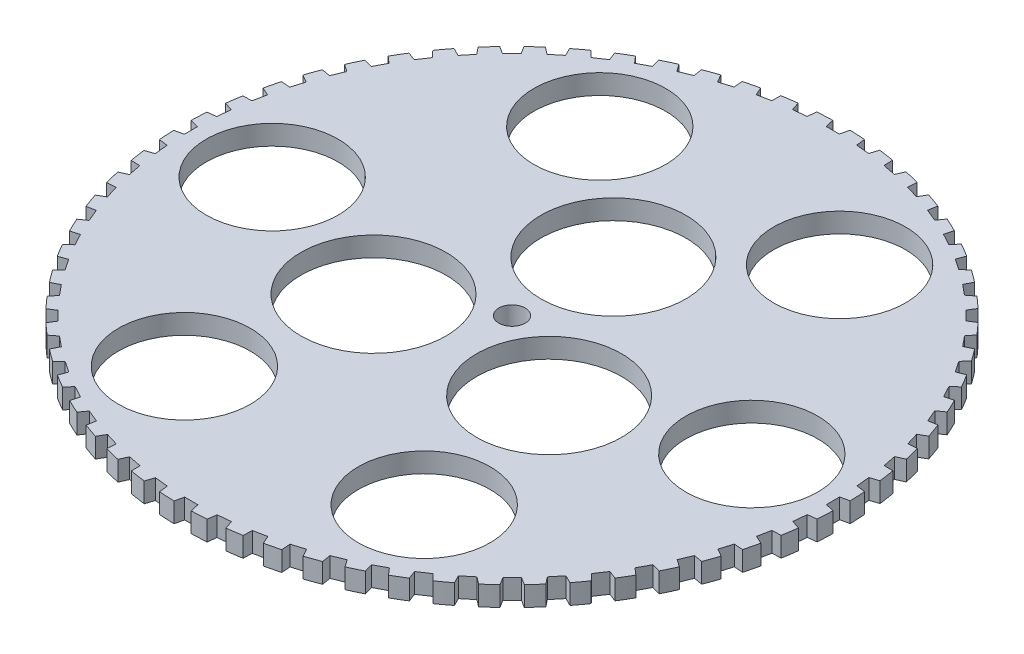
SolidWorks part; units mm, degrees
ref_plane "Plan de face" through (0, 0, 0) normal (0, 0, 1) x (1, 0, 0)
ref_plane "Plan de dessus" through (0, 0, 0) normal (0, 1, 0) x (1, 0, 0)
ref_plane "Plan de droite" through (0, 0, 0) normal (1, 0, 0) x (0, 0, -1)
sketch "Esquisse1" plane through (0, 0, 0) normal (0, 1, 0) x (1, 0, 0)
  circle A0 centre (0, 0) radius 50
  circle A1 centre (36.3777, 0) radius 10
  circle A2 centre (18.1888, -31.504) radius 10
  circle A3 centre (-18.1888, -31.504) radius 10
  circle A4 centre (-36.3777, 0) radius 10
  circle A5 centre (-18.1888, 31.504) radius 10
  circle A6 centre (18.1888, 31.504) radius 10
  circle A7 centre (0, 15.3792) radius 11
  circle A8 centre (13.3188, -7.6896) radius 11
  circle A9 centre (-13.3188, -7.6896) radius 11
  circle A10 centre (0, 0) radius 2
  dimension "D1" = 100
extrude "Extrusion1" add sketch "Esquisse1" along normal blind 3
sketch "Esquisse3" plane through (0, 3, 0) normal (0, 1, 0) x (1, 0, 0)
  line L0 (-3.4533, -50.9425) -> (-6.5125, -50.6412)
  line L1 (1.022, -48.6717) -> (-0.9823, -48.6717)
  line L2 (1.022, -48.6717) -> (1.5566, -51.0357)
  line L3 (1.5566, -51.0357) -> (-1.5174, -51.0357)
  line L4 (-0.9823, -48.6717) -> (-1.5174, -51.0357)
  line L5 (-5.7482, -48.341) -> (-6.5125, -50.6412)
  line L6 (-3.7536, -48.5375) -> (-5.7482, -48.341)
  line L7 (-3.7536, -48.5375) -> (-3.4533, -50.9425)
  line L8 (-8.4299, -50.3587) -> (-11.4448, -49.759)
  line L9 (-10.4588, -47.5448) -> (-11.4448, -49.759)
  line L10 (-8.4931, -47.9358) -> (-10.4588, -47.5448)
  line L11 (-8.4931, -47.9358) -> (-8.4299, -50.3587)
  line L12 (-13.3253, -49.2899) -> (-16.2669, -48.3976)
  line L13 (-15.0686, -46.2908) -> (-16.2669, -48.3976)
  line L14 (-13.1507, -46.8726) -> (-15.0686, -46.2908)
  line L15 (-13.1507, -46.8726) -> (-13.3253, -49.2899)
  line L16 (-18.0924, -47.7465) -> (-20.9324, -46.5701)
  line L17 (-19.5334, -44.5909) -> (-20.9324, -46.5701)
  line L18 (-17.6817, -45.3579) -> (-19.5334, -44.5909)
  line L19 (-17.6817, -45.3579) -> (-18.0924, -47.7465)
  line L20 (-22.6853, -45.7432) -> (-25.3963, -44.2941)
  line L21 (-23.81, -42.4615) -> (-25.3963, -44.2941)
  line L22 (-22.0424, -43.4063) -> (-23.81, -42.4615)
  line L23 (-22.0424, -43.4063) -> (-22.6853, -45.7432)
  line L24 (-27.0597, -43.2994) -> (-29.6156, -41.5916)
  line L25 (-27.8573, -39.9233) -> (-29.6156, -41.5916)
  line L26 (-26.1908, -41.0368) -> (-27.8573, -39.9233)
  line L27 (-26.1908, -41.0368) -> (-27.0597, -43.2994)
  line L28 (-31.1735, -40.4386) -> (-33.5497, -38.4885)
  line L29 (-31.6363, -37.0006) -> (-33.5497, -38.4885)
  line L30 (-30.087, -38.272) -> (-31.6363, -37.0006)
  line L31 (-30.087, -38.272) -> (-31.1735, -40.4386)
  line L32 (-34.987, -37.1883) -> (-37.1606, -35.0147)
  line L33 (-35.1107, -33.7215) -> (-37.1606, -35.0147)
  line L34 (-33.6934, -35.1387) -> (-35.1107, -33.7215)
  line L35 (-33.6934, -35.1387) -> (-34.987, -37.1883)
  line L36 (-38.4636, -33.5799) -> (-40.4137, -31.2037)
  line L37 (-38.2469, -30.1177) -> (-40.4137, -31.2037)
  line L38 (-36.9754, -31.667) -> (-38.2469, -30.1177)
  line L39 (-36.9754, -31.667) -> (-38.4636, -33.5799)
  line L40 (-41.5698, -29.6481) -> (-43.2776, -27.0922)
  line L41 (-41.0148, -26.2238) -> (-43.2776, -27.0922)
  line L42 (-39.9013, -27.8903) -> (-41.0148, -26.2238)
  line L43 (-39.9013, -27.8903) -> (-41.5698, -29.6481)
  line L44 (-44.2757, -25.4308) -> (-45.7247, -22.7198)
  line L45 (-43.3876, -22.0774) -> (-45.7247, -22.7198)
  line L46 (-42.4428, -23.845) -> (-43.3876, -22.0774)
  line L47 (-42.4428, -23.845) -> (-44.2757, -25.4308)
  line L48 (-46.5551, -20.9686) -> (-47.7315, -18.1286)
  line L49 (-45.3427, -17.7183) -> (-47.7315, -18.1286)
  line L50 (-44.5757, -19.57) -> (-45.3427, -17.7183)
  line L51 (-44.5757, -19.57) -> (-46.5551, -20.9686)
  line L52 (-48.3863, -16.3044) -> (-49.2786, -13.3628)
  line L53 (-46.861, -13.1886) -> (-49.2786, -13.3628)
  line L54 (-46.2792, -15.1066) -> (-46.861, -13.1886)
  line L55 (-46.2792, -15.1066) -> (-48.3863, -16.3044)
  line L56 (-49.7514, -11.4832) -> (-50.3511, -8.4683)
  line L57 (-47.9281, -8.532) -> (-50.3511, -8.4683)
  line L58 (-47.5371, -10.4977) -> (-47.9281, -8.532)
  line L59 (-47.5371, -10.4977) -> (-49.7514, -11.4832)
  line L60 (-50.6374, -6.5514) -> (-50.9387, -3.4923)
  line L61 (-48.5336, -3.7931) -> (-50.9387, -3.4923)
  line L62 (-48.3371, -5.7877) -> (-48.5336, -3.7931)
  line L63 (-48.3371, -5.7877) -> (-50.6374, -6.5514)
  line L64 (-51.0357, -1.5566) -> (-51.0357, 1.5174)
  line L65 (-48.6717, 0.9823) -> (-51.0357, 1.5174)
  line L66 (-48.6717, -1.022) -> (-48.6717, 0.9823)
  line L67 (-48.6717, -1.022) -> (-51.0357, -1.5566)
  line L68 (-50.9425, 3.4533) -> (-50.6412, 6.5125)
  line L69 (-48.341, 5.7482) -> (-50.6412, 6.5125)
  line L70 (-48.5375, 3.7536) -> (-48.341, 5.7482)
  line L71 (-48.5375, 3.7536) -> (-50.9425, 3.4533)
  line L72 (-50.3587, 8.4299) -> (-49.759, 11.4448)
  line L73 (-47.5448, 10.4588) -> (-49.759, 11.4448)
  line L74 (-47.9358, 8.4931) -> (-47.5448, 10.4588)
  line L75 (-47.9358, 8.4931) -> (-50.3587, 8.4299)
  line L76 (-49.2899, 13.3253) -> (-48.3976, 16.2669)
  line L77 (-46.2908, 15.0686) -> (-48.3976, 16.2669)
  line L78 (-46.8726, 13.1507) -> (-46.2908, 15.0686)
  line L79 (-46.8726, 13.1507) -> (-49.2899, 13.3253)
  line L80 (-47.7465, 18.0924) -> (-46.5701, 20.9324)
  line L81 (-44.5909, 19.5334) -> (-46.5701, 20.9324)
  line L82 (-45.3579, 17.6817) -> (-44.5909, 19.5334)
  line L83 (-45.3579, 17.6817) -> (-47.7465, 18.0924)
  line L84 (-45.7432, 22.6853) -> (-44.2941, 25.3963)
  line L85 (-42.4615, 23.81) -> (-44.2941, 25.3963)
  line L86 (-43.4063, 22.0424) -> (-42.4615, 23.81)
  line L87 (-43.4063, 22.0424) -> (-45.7432, 22.6853)
  line L88 (-43.2994, 27.0597) -> (-41.5916, 29.6156)
  line L89 (-39.9233, 27.8573) -> (-41.5916, 29.6156)
  line L90 (-41.0368, 26.1908) -> (-39.9233, 27.8573)
  line L91 (-41.0368, 26.1908) -> (-43.2994, 27.0597)
  line L92 (-40.4386, 31.1735) -> (-38.4885, 33.5497)
  line L93 (-37.0006, 31.6363) -> (-38.4885, 33.5497)
  line L94 (-38.272, 30.087) -> (-37.0006, 31.6363)
  line L95 (-38.272, 30.087) -> (-40.4386, 31.1735)
  line L96 (-37.1883, 34.987) -> (-35.0147, 37.1606)
  line L97 (-33.7215, 35.1107) -> (-35.0147, 37.1606)
  line L98 (-35.1387, 33.6934) -> (-33.7215, 35.1107)
  line L99 (-35.1387, 33.6934) -> (-37.1883, 34.987)
  line L100 (-33.5799, 38.4636) -> (-31.2037, 40.4137)
  line L101 (-30.1177, 38.2469) -> (-31.2037, 40.4137)
  line L102 (-31.667, 36.9754) -> (-30.1177, 38.2469)
  line L103 (-31.667, 36.9754) -> (-33.5799, 38.4636)
  line L104 (-29.6481, 41.5698) -> (-27.0922, 43.2776)
  line L105 (-26.2238, 41.0148) -> (-27.0922, 43.2776)
  line L106 (-27.8903, 39.9013) -> (-26.2238, 41.0148)
  line L107 (-27.8903, 39.9013) -> (-29.6481, 41.5698)
  line L108 (-25.4308, 44.2757) -> (-22.7198, 45.7247)
  line L109 (-22.0774, 43.3876) -> (-22.7198, 45.7247)
  line L110 (-23.845, 42.4428) -> (-22.0774, 43.3876)
  line L111 (-23.845, 42.4428) -> (-25.4308, 44.2757)
  line L112 (-20.9686, 46.5551) -> (-18.1286, 47.7315)
  line L113 (-17.7183, 45.3427) -> (-18.1286, 47.7315)
  line L114 (-19.57, 44.5757) -> (-17.7183, 45.3427)
  line L115 (-19.57, 44.5757) -> (-20.9686, 46.5551)
  line L116 (-16.3044, 48.3863) -> (-13.3628, 49.2786)
  line L117 (-13.1886, 46.861) -> (-13.3628, 49.2786)
  line L118 (-15.1066, 46.2792) -> (-13.1886, 46.861)
  line L119 (-15.1066, 46.2792) -> (-16.3044, 48.3863)
  line L120 (-11.4832, 49.7514) -> (-8.4683, 50.3511)
  line L121 (-8.532, 47.9281) -> (-8.4683, 50.3511)
  line L122 (-10.4977, 47.5371) -> (-8.532, 47.9281)
  line L123 (-10.4977, 47.5371) -> (-11.4832, 49.7514)
  line L124 (-6.5514, 50.6374) -> (-3.4923, 50.9387)
  line L125 (-3.7931, 48.5336) -> (-3.4923, 50.9387)
  line L126 (-5.7877, 48.3371) -> (-3.7931, 48.5336)
  line L127 (-5.7877, 48.3371) -> (-6.5514, 50.6374)
  line L128 (-1.5566, 51.0357) -> (1.5174, 51.0357)
  line L129 (0.9823, 48.6717) -> (1.5174, 51.0357)
  line L130 (-1.022, 48.6717) -> (0.9823, 48.6717)
  line L131 (-1.022, 48.6717) -> (-1.5566, 51.0357)
  line L132 (3.4533, 50.9425) -> (6.5125, 50.6412)
  line L133 (5.7482, 48.341) -> (6.5125, 50.6412)
  line L134 (3.7536, 48.5375) -> (5.7482, 48.341)
  line L135 (3.7536, 48.5375) -> (3.4533, 50.9425)
  line L136 (8.4299, 50.3587) -> (11.4448, 49.759)
  line L137 (10.4588, 47.5448) -> (11.4448, 49.759)
  line L138 (8.4931, 47.9358) -> (10.4588, 47.5448)
  line L139 (8.4931, 47.9358) -> (8.4299, 50.3587)
  line L140 (13.3253, 49.2899) -> (16.2669, 48.3976)
  line L141 (15.0686, 46.2908) -> (16.2669, 48.3976)
  line L142 (13.1507, 46.8726) -> (15.0686, 46.2908)
  line L143 (13.1507, 46.8726) -> (13.3253, 49.2899)
  line L144 (18.0924, 47.7465) -> (20.9324, 46.5701)
  line L145 (19.5334, 44.5909) -> (20.9324, 46.5701)
  line L146 (17.6817, 45.3579) -> (19.5334, 44.5909)
  line L147 (17.6817, 45.3579) -> (18.0924, 47.7465)
  line L148 (22.6853, 45.7432) -> (25.3963, 44.2941)
  line L149 (23.81, 42.4615) -> (25.3963, 44.2941)
  line L150 (22.0424, 43.4063) -> (23.81, 42.4615)
  line L151 (22.0424, 43.4063) -> (22.6853, 45.7432)
  line L152 (27.0597, 43.2994) -> (29.6156, 41.5916)
  line L153 (27.8573, 39.9233) -> (29.6156, 41.5916)
  line L154 (26.1908, 41.0368) -> (27.8573, 39.9233)
  line L155 (26.1908, 41.0368) -> (27.0597, 43.2994)
  line L156 (31.1735, 40.4386) -> (33.5497, 38.4885)
  line L157 (31.6363, 37.0006) -> (33.5497, 38.4885)
  line L158 (30.087, 38.272) -> (31.6363, 37.0006)
  line L159 (30.087, 38.272) -> (31.1735, 40.4386)
  line L160 (34.987, 37.1883) -> (37.1606, 35.0147)
  line L161 (35.1107, 33.7215) -> (37.1606, 35.0147)
  line L162 (33.6934, 35.1387) -> (35.1107, 33.7215)
  line L163 (33.6934, 35.1387) -> (34.987, 37.1883)
  line L164 (38.4636, 33.5799) -> (40.4137, 31.2037)
  line L165 (38.2469, 30.1177) -> (40.4137, 31.2037)
  line L166 (36.9754, 31.667) -> (38.2469, 30.1177)
  line L167 (36.9754, 31.667) -> (38.4636, 33.5799)
  line L168 (41.5698, 29.6481) -> (43.2776, 27.0922)
  line L169 (41.0148, 26.2238) -> (43.2776, 27.0922)
  line L170 (39.9013, 27.8903) -> (41.0148, 26.2238)
  line L171 (39.9013, 27.8903) -> (41.5698, 29.6481)
  line L172 (44.2757, 25.4308) -> (45.7247, 22.7198)
  line L173 (43.3876, 22.0774) -> (45.7247, 22.7198)
  line L174 (42.4428, 23.845) -> (43.3876, 22.0774)
  line L175 (42.4428, 23.845) -> (44.2757, 25.4308)
  line L176 (46.5551, 20.9686) -> (47.7315, 18.1286)
  line L177 (45.3427, 17.7183) -> (47.7315, 18.1286)
  line L178 (44.5757, 19.57) -> (45.3427, 17.7183)
  line L179 (44.5757, 19.57) -> (46.5551, 20.9686)
  line L180 (48.3863, 16.3044) -> (49.2786, 13.3628)
  line L181 (46.861, 13.1886) -> (49.2786, 13.3628)
  line L182 (46.2792, 15.1066) -> (46.861, 13.1886)
  line L183 (46.2792, 15.1066) -> (48.3863, 16.3044)
  line L184 (49.7514, 11.4832) -> (50.3511, 8.4683)
  line L185 (47.9281, 8.532) -> (50.3511, 8.4683)
  line L186 (47.5371, 10.4977) -> (47.9281, 8.532)
  line L187 (47.5371, 10.4977) -> (49.7514, 11.4832)
  line L188 (50.6374, 6.5514) -> (50.9387, 3.4923)
  line L189 (48.5336, 3.7931) -> (50.9387, 3.4923)
  line L190 (48.3371, 5.7877) -> (48.5336, 3.7931)
  line L191 (48.3371, 5.7877) -> (50.6374, 6.5514)
  line L192 (51.0357, 1.5566) -> (51.0357, -1.5174)
  line L193 (48.6717, -0.9823) -> (51.0357, -1.5174)
  line L194 (48.6717, 1.022) -> (48.6717, -0.9823)
  line L195 (48.6717, 1.022) -> (51.0357, 1.5566)
  line L196 (50.9425, -3.4533) -> (50.6412, -6.5125)
  line L197 (48.341, -5.7482) -> (50.6412, -6.5125)
  line L198 (48.5375, -3.7536) -> (48.341, -5.7482)
  line L199 (48.5375, -3.7536) -> (50.9425, -3.4533)
  line L200 (50.3587, -8.4299) -> (49.759, -11.4448)
  line L201 (47.5448, -10.4588) -> (49.759, -11.4448)
  line L202 (47.9358, -8.4931) -> (47.5448, -10.4588)
  line L203 (47.9358, -8.4931) -> (50.3587, -8.4299)
  line L204 (49.2899, -13.3253) -> (48.3976, -16.2669)
  line L205 (46.2908, -15.0686) -> (48.3976, -16.2669)
  line L206 (46.8726, -13.1507) -> (46.2908, -15.0686)
  line L207 (46.8726, -13.1507) -> (49.2899, -13.3253)
  line L208 (47.7465, -18.0924) -> (46.5701, -20.9324)
  line L209 (44.5909, -19.5334) -> (46.5701, -20.9324)
  line L210 (45.3579, -17.6817) -> (44.5909, -19.5334)
  line L211 (45.3579, -17.6817) -> (47.7465, -18.0924)
  line L212 (45.7432, -22.6853) -> (44.2941, -25.3963)
  line L213 (42.4615, -23.81) -> (44.2941, -25.3963)
  line L214 (43.4063, -22.0424) -> (42.4615, -23.81)
  line L215 (43.4063, -22.0424) -> (45.7432, -22.6853)
  line L216 (43.2994, -27.0597) -> (41.5916, -29.6156)
  line L217 (39.9233, -27.8573) -> (41.5916, -29.6156)
  line L218 (41.0368, -26.1908) -> (39.9233, -27.8573)
  line L219 (41.0368, -26.1908) -> (43.2994, -27.0597)
  line L220 (40.4386, -31.1735) -> (38.4885, -33.5497)
  line L221 (37.0006, -31.6363) -> (38.4885, -33.5497)
  line L222 (38.272, -30.087) -> (37.0006, -31.6363)
  line L223 (38.272, -30.087) -> (40.4386, -31.1735)
  line L224 (37.1883, -34.987) -> (35.0147, -37.1606)
  line L225 (33.7215, -35.1107) -> (35.0147, -37.1606)
  line L226 (35.1387, -33.6934) -> (33.7215, -35.1107)
  line L227 (35.1387, -33.6934) -> (37.1883, -34.987)
  line L228 (33.5799, -38.4636) -> (31.2037, -40.4137)
  line L229 (30.1177, -38.2469) -> (31.2037, -40.4137)
  line L230 (31.667, -36.9754) -> (30.1177, -38.2469)
  line L231 (31.667, -36.9754) -> (33.5799, -38.4636)
  line L232 (29.6481, -41.5698) -> (27.0922, -43.2776)
  line L233 (26.2238, -41.0148) -> (27.0922, -43.2776)
  line L234 (27.8903, -39.9013) -> (26.2238, -41.0148)
  line L235 (27.8903, -39.9013) -> (29.6481, -41.5698)
  line L236 (25.4308, -44.2757) -> (22.7198, -45.7247)
  line L237 (22.0774, -43.3876) -> (22.7198, -45.7247)
  line L238 (23.845, -42.4428) -> (22.0774, -43.3876)
  line L239 (23.845, -42.4428) -> (25.4308, -44.2757)
  line L240 (20.9686, -46.5551) -> (18.1286, -47.7315)
  line L241 (17.7183, -45.3427) -> (18.1286, -47.7315)
  line L242 (19.57, -44.5757) -> (17.7183, -45.3427)
  line L243 (19.57, -44.5757) -> (20.9686, -46.5551)
  line L244 (16.3044, -48.3863) -> (13.3628, -49.2786)
  line L245 (13.1886, -46.861) -> (13.3628, -49.2786)
  line L246 (15.1066, -46.2792) -> (13.1886, -46.861)
  line L247 (15.1066, -46.2792) -> (16.3044, -48.3863)
  line L248 (11.4832, -49.7514) -> (8.4683, -50.3511)
  line L249 (8.532, -47.9281) -> (8.4683, -50.3511)
  line L250 (10.4977, -47.5371) -> (8.532, -47.9281)
  line L251 (10.4977, -47.5371) -> (11.4832, -49.7514)
  line L252 (6.5514, -50.6374) -> (3.4923, -50.9387)
  line L253 (3.7931, -48.5336) -> (3.4923, -50.9387)
  line L254 (5.7877, -48.3371) -> (3.7931, -48.5336)
  line L255 (5.7877, -48.3371) -> (6.5514, -50.6374)
extrude "Enlèv. mat.-Extru.1" cut sketch "Esquisse3" against normal up to next (3 mm away)
